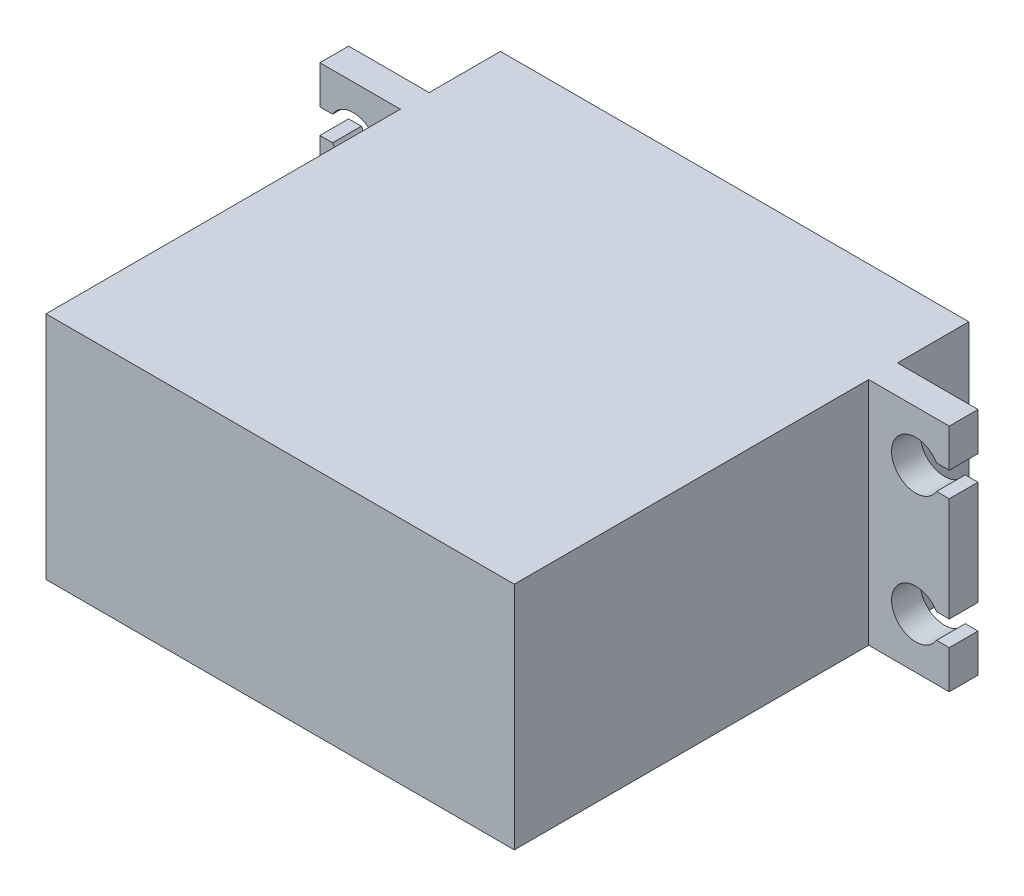
SolidWorks part; units mm, degrees
ref_plane "Front Plane" through (0, 0, 0) normal (0, 0, 1) x (1, 0, 0)
ref_plane "Top Plane" through (0, 0, 0) normal (0, 1, 0) x (1, 0, 0)
ref_plane "Right Plane" through (0, 0, 0) normal (1, 0, 0) x (0, 0, -1)
sketch "Sketch1" plane through (0, 0, 0) normal (0, 1, 0) x (1, 0, 0)
  line L1 (20.35, 19.75) -> (-20.35, 19.75)
  line L2 (20.35, 19.75) -> (20.35, -19.75)
  line L3 (20.35, -19.75) -> (-20.35, -19.75)
  line L4 (-20.35, 19.75) -> (-20.35, -19.75)
  line L5 (20.35, 19.75) -> (-20.35, -19.75) construction
  line L6 (20.35, -19.75) -> (-20.35, 19.75) construction
  point P0 (0, 0)
  dimension "D1" = 40.7
  dimension "D2" = 39.5
extrude "Boss-Extrude1" add sketch "Sketch1" along normal mid plane 20
sketch "Sketch2" plane through (20.35, 0, 0) normal (1, 0, 0) x (0, 0, -1)
  line L0 (-19.75, 10) -> (19.75, 10) construction
  line L1 (11.05, 10) -> (13.55, 10)
  line L2 (11.05, 10) -> (11.05, -10)
  line L3 (11.05, -10) -> (13.55, -10)
  line L4 (13.55, 10) -> (13.55, -10)
  line L5 (-19.75, -10) -> (19.75, -10) construction
  line L6 (19.75, 10) -> (19.75, -10) construction
  dimension "D1" = 8.7
  dimension "D2" = 2.5
extrude "Boss-Extrude2" add sketch "Sketch2" along normal blind 7
sketch "Sketch9" plane through (0, 0, 0) normal (0, 1, 0) x (1, 0, 0)
  line L0 (20.35, 13.55) -> (20.35, 14.65)
  line L2 (20.35, 13.55) -> (20.35, 19.75) construction
  line L3 (20.35, 14.65) -> (27.35, 13.55)
  line L4 (27.35, 13.55) -> (20.35, 13.55)
  dimension "D1" = 1.1
extrude "Boss-Extrude5" add sketch "Sketch9" along normal mid plane 1
mirror "Mirror1" about plane through (0, 0, 0) normal (1, 0, 0) of "Boss-Extrude5", "Boss-Extrude2"
sketch "Sketch3" plane through (0, 0, -13.55) normal (0, 0, -1) x (-1, 0, 0)
  line L0 (0, 0) -> (0, 13.6101) construction
  line L10 (-27.35, 10) -> (-20.35, 10) construction
  line L13 (-22.34, 5.6) -> (22.34, 5.6) construction
  line L14 (-26.244, 6.675) -> (-27.35, 6.675)
  line L15 (-27.35, -10) -> (-27.35, -0.5) construction
  line L16 (-27.35, 6.675) -> (-27.35, 4.525)
  line L17 (-27.35, 4.525) -> (-26.244, 4.525)
  line L18 (26.244, 6.675) -> (27.35, 6.675)
  line L19 (27.35, 6.675) -> (27.35, 4.525)
  line L20 (27.35, 4.525) -> (26.244, 4.525)
  arc A2 (-26.244, 4.525) -> (-26.244, 6.675) centre (-24.44, 5.6) ccw
  arc A5 (26.244, 4.525) -> (26.244, 6.675) centre (24.44, 5.6) cw
  point P8 (-24.44, 7.7)
  point P17 (-22.34, 5.6)
  point P18 (22.34, 5.6)
  dimension "D1" = 4.2
  dimension "D2" = 2.3
  dimension "D4" = 44.68
  dimension "D5" = 2.15
extrude "Cut-Extrude1" cut sketch "Sketch3" against normal through all
mirror "Mirror2" about plane through (0, 0, 0) normal (0, 1, 0) of "Cut-Extrude1"
sketch "Sketch4" plane through (0, 0, -19.75) normal (0, 0, -1) x (-1, 0, 0)
  line L2 (-20.35, -10) -> (-20.35, -0.5) construction
  circle A0 centre (-10.62, 0) radius 6.57
  point P2 (-4.05, 0)
  dimension "D1" = 13.14
  dimension "D2" = 16.3
extrude "Boss-Extrude3" add sketch "Sketch4" along normal blind 1.5
sketch "Sketch5" plane through (0, 0, -21.25) normal (0, 0, -1) x (-1, 0, 0)
  circle A0 centre (-10.62, 0) radius 3
  dimension "D1" = 6
extrude "Boss-Extrude4" add sketch "Sketch5" along normal blind 4.2
hole_wizard "M3x0.5 Tapped Hole1" positions "Sketch8" profile "Sketch7" tap size "M3x0.5" standard "ANSI Metric"
sketch "Sketch8" plane through (0, 0, -25.45) normal (0, 0, -1) x (-1, 0, 0)
  point P0 (-10.62, 0)
sketch "Sketch7" plane through (10.62, 0, -25.45) normal (1, 0, 0) x (0, 1, 0)
  line L0 (0, 0) -> (0, 5.7511)
  line L1 (0, 5.7511) -> (1.25, 5)
  line L2 (1.25, 5) -> (1.25, 0.275)
  line L3 (1.25, 0.275) -> (1.525, 0)
  line L5 (1.525, 0) -> (0, 0)
  line L6 (-1.25, 0.275) -> (-1.525, 0) construction
  line L10 (0, 5.7511) -> (-1.25, 5) construction
  line L11 (0, -6.35) -> (0, 107.95) construction
  dimension "Tap Drill Dia." = 2.5
  dimension "Tap Drill Depth" = 5
  dimension "Near C'Sink Dia." = 3.05
  dimension "Near C'Sink Angle" = 90
  dimension "Drill Angle" = 118
cosmetic thread "Hole Thread1" parameters "D1"=6, "D2"=3
